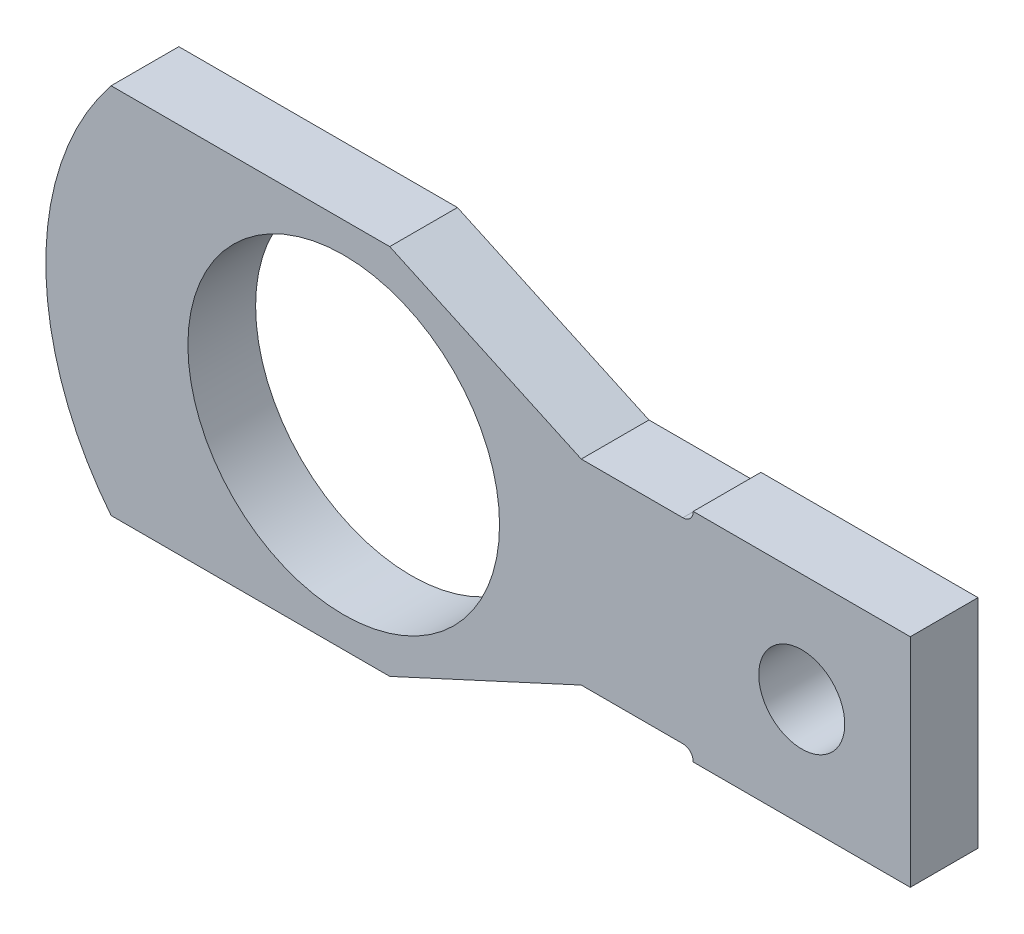
SolidWorks part; units mm, degrees
material "Aleación 1060"
ref_plane "Alzado" through (0, 0, 0) normal (0, 0, 1) x (1, 0, 0)
ref_plane "Planta" through (0, 0, 0) normal (0, 1, 0) x (1, 0, 0)
ref_plane "Vista lateral" through (0, 0, 0) normal (1, 0, 0) x (0, 0, -1)
sketch "Croquis1" plane through (0, 0, 0) normal (0, 0, 1) x (1, 0, 0)
  line L0 (-72.263, -175.3957) -> (-72.263, -249.0557)
  line L1 (0, 219.964) -> (0, -418.338) construction
  line L2 (-137.414, -33.9798) -> (-72.263, -175.3957)
  line L3 (-137.414, 171.7602) -> (-137.414, -33.9798)
  line L4 (137.414, 171.7602) -> (137.414, -33.9798)
  line L5 (0, -418.338) -> (0, -338.201) construction
  line L6 (-72.263, -250.444) -> (-72.263, -249.0557)
  line L7 (-80.137, -258.064) -> (-79.883, -258.064)
  line L8 (-80.137, -258.064) -> (-80.137, -418.338)
  line L9 (-80.137, -418.338) -> (80.137, -418.338)
  line L10 (80.137, -258.064) -> (80.137, -418.338)
  line L11 (-80.137, -258.064) -> (80.137, -418.338) construction
  line L12 (-80.137, -418.338) -> (80.137, -258.064) construction
  line L13 (72.263, -250.444) -> (72.263, -249.0557)
  line L14 (72.263, -175.3957) -> (72.263, -249.0557)
  line L15 (137.414, -33.9798) -> (72.263, -175.3957)
  line L16 (79.883, -258.064) -> (80.137, -258.064)
  circle A0 centre (0, 0) radius 115.062
  circle A1 centre (0, 0) radius 122.936
  arc A2 (137.414, 171.7602) -> (-137.414, 171.7602) centre (0, 0) ccw
  circle A3 centre (0, 122.936) radius 3.937
  circle A4 centre (106.4657, 61.468) radius 3.937
  circle A5 centre (0, 0) radius 122.936
  circle A6 centre (106.4657, -61.468) radius 3.937
  circle A7 centre (0, 0) radius 122.936
  circle A8 centre (0, -122.936) radius 3.937
  circle A9 centre (0, 0) radius 122.936
  circle A10 centre (-106.4657, -61.468) radius 3.937
  circle A11 centre (0, 0) radius 122.936
  circle A12 centre (-106.4657, 61.468) radius 3.937
  circle A13 centre (0, 0) radius 122.936
  arc A14 (72.263, -250.444) -> (79.883, -258.064) centre (79.883, -250.444) ccw
  arc A15 (-72.263, -250.444) -> (-79.883, -258.064) centre (-79.883, -250.444) cw
  circle A16 centre (0, -338.201) radius 31.75
  point P25 (0, 0)
  point P41 (72.263, -258.064)
  point P44 (-72.263, -258.064)
  dimension "D1" = 230.124
  dimension "D2" = 245.872
  dimension "D3" = 439.928
  dimension "D4" = 7.874
  dimension "D7" = 638.302
  dimension "D9" = 7.62
  dimension "D16" = 63.5
  dimension "D6" = 155.702
  dimension "D8" = 205.74
  dimension "D10" = 73.66
  dimension "D11" = 80.137
  dimension "D12" = 160.274
  dimension "D13" = 160.274
  dimension "D14" = 274.828
  dimension "D15" = 7.874
  dimension "D5" = 6
extrude "Saliente-Extruir1" add sketch "Croquis1" along normal blind 50 contours A2 L3 L2 L0 L6 A15 L7 L8 L9 L10 L16 A14 L13 L14 L15 L4 | A16 | A0
move or copy body "Corps-Déplacer/Copier1" bodies to move or copy 104 copy no rotation origin (0, 0, 0) rotation axis (0, 0, 1) rotation angle 90
